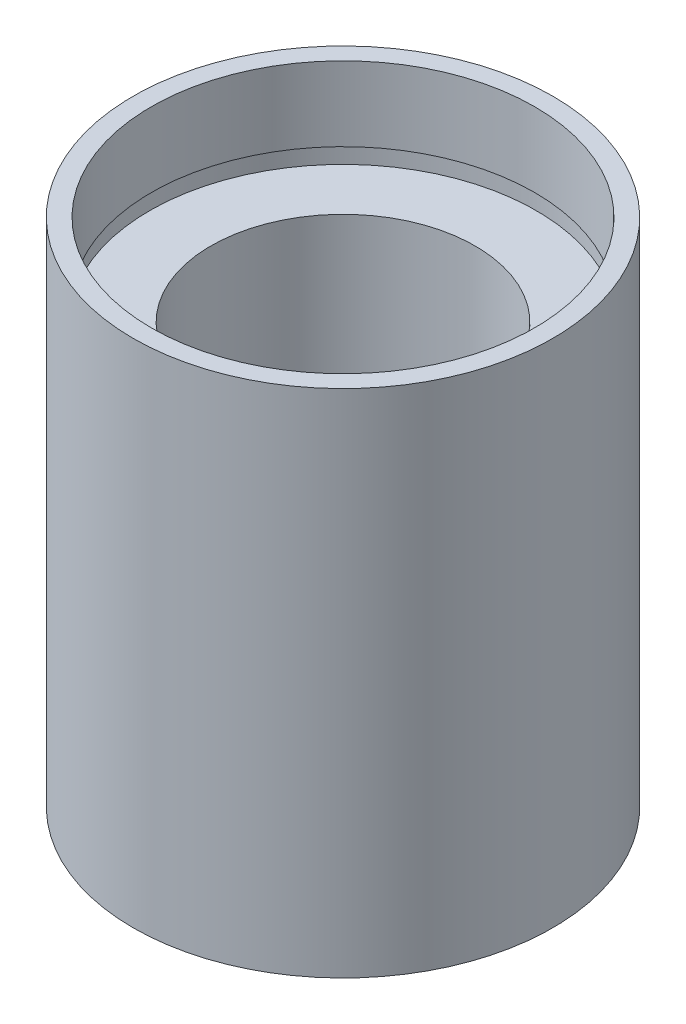
SolidWorks part; units mm, degrees
ref_plane "前视基准面" through (0, 0, 0) normal (0, 0, 1) x (1, 0, 0)
ref_plane "上视基准面" through (0, 0, 0) normal (0, 1, 0) x (1, 0, 0)
ref_plane "右视基准面" through (0, 0, 0) normal (1, 0, 0) x (0, 0, -1)
sketch "草图1" plane through (0, 0, 0) normal (0, 0, 1) x (1, 0, 0)
  line L0 (0, 161.3762) -> (0, 0) construction
  line L1 (141.7365, 0) -> (-131.7984, 0) construction
  line L2 (11.1, 0) -> (11.1, 4.5)
  line L3 (11.7, 4.5) -> (11.7, 5.5)
  line L4 (11.1, 4.5) -> (11.7, 4.5)
  line L5 (8, 5.5) -> (8, 25.4)
  line L6 (11.7, 5.5) -> (8, 5.5)
  line L7 (12.7, 0) -> (12.7, 30.9)
  line L8 (11.1, 0) -> (12.7, 0)
  line L9 (11.6, 30.9) -> (11.6, 26.4)
  line L10 (11.6, 30.9) -> (12.7, 30.9)
  line L11 (11.7, 26.4) -> (11.7, 25.4)
  line L12 (11.6, 26.4) -> (11.7, 26.4)
  line L13 (8, 25.4) -> (11.7, 25.4)
  point P15 (11.6, 28.65)
  dimension "D1" = 11.1
  dimension "D2" = 4.5
  dimension "D3" = 11.7
  dimension "D4" = 8
  dimension "D5" = 12.7
  dimension "D6" = 11.6
  dimension "D7" = 4.5
  dimension "D8" = 11.7
  dimension "D9" = 5.5
  dimension "D10" = 1
  dimension "D11" = 25.4
revolve "旋转1" add sketch "草图1" angle 360 about L0
cosmetic thread "装饰螺纹线1"
cosmetic thread "装饰螺纹线2"
cosmetic thread "装饰螺纹线3"
